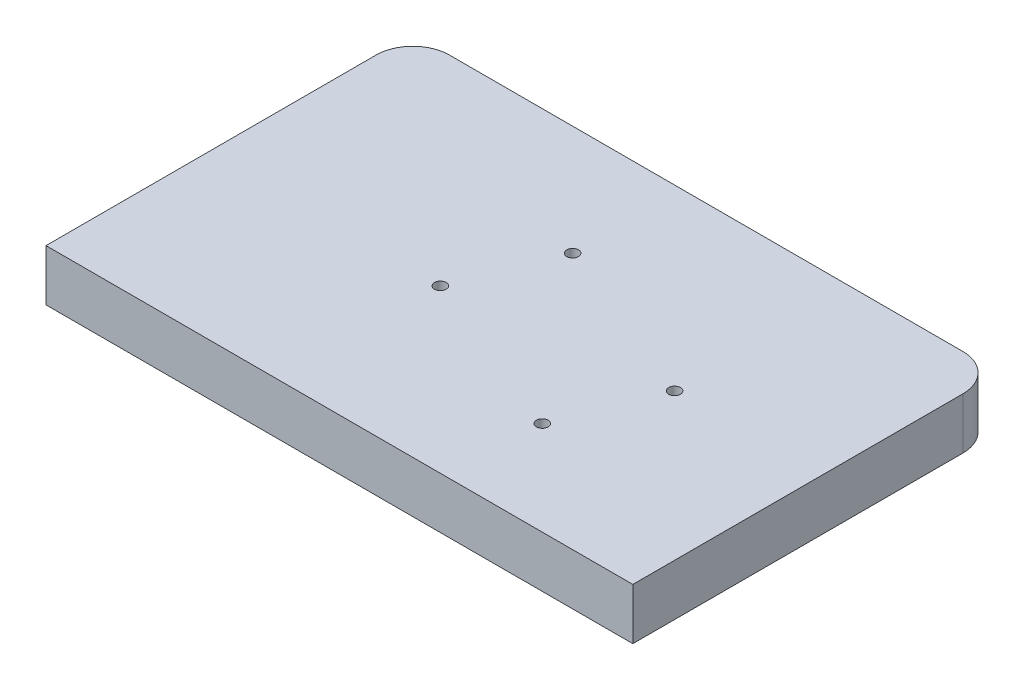
SolidWorks part; units mm, degrees
material "Pine"
ref_plane "Front Plane" through (0, 0, 0) normal (0, 0, 1) x (1, 0, 0)
ref_plane "Top Plane" through (0, 0, 0) normal (0, 1, 0) x (1, 0, 0)
ref_plane "Right Plane" through (0, 0, 0) normal (1, 0, 0) x (0, 0, -1)
sketch "Sketch2" plane through (0, 0, 0) normal (0, 1, 0) x (1, 0, 0)
  line L1 (-101.6, 63.5) -> (101.6, 63.5)
  line L2 (-101.6, 63.5) -> (-101.6, -63.5)
  line L3 (-101.6, -63.5) -> (101.6, -63.5)
  line L4 (101.6, 63.5) -> (101.6, -63.5)
  line L5 (-101.6, 63.5) -> (101.6, -63.5) construction
  line L6 (-101.6, -63.5) -> (101.6, 63.5) construction
  point P0 (0, 0)
  dimension "D1" = 203.2
  dimension "D2" = 127
extrude "Boss-Extrude2" add sketch "Sketch2" along normal blind 17.78
fillet "Fillet1" radius 12.7 2 edges at (-101.6, 8.89, -63.5) (101.6, 8.89, -63.5)
sketch "Sketch5" plane through (0, 0, 0) normal (0, -1, 0) x (1, 0, 0)
  line L0 (-101.6, 63.5) -> (101.6, 63.5) construction
  line L1 (101.6, 63.5) -> (101.6, -50.8) construction
  line L2 (-101.6, -50.8) -> (-101.6, 63.5) construction
  circle A0 centre (50.8, 49.8348) radius 2.0828
  circle A1 centre (33.5788, 25.0698) radius 2.0828
  circle A2 centre (-50.8, 25.0698) radius 2.0828
  circle A3 centre (-33.5788, 49.8348) radius 2.0828
  dimension "D1" = 4.1656
  dimension "D2" = 13.6652
  dimension "D3" = 38.4302
  dimension "D4" = 17.2212
  dimension "D5" = 38.4302
  dimension "D6" = 13.6652
  dimension "D7" = 17.2212
  dimension "D8" = 50.8
  dimension "D9" = 50.8
extrude "Cut-Extrude2" cut sketch "Sketch5" against normal blind 12.7
sketch "Sketch6" plane through (0, 17.78, 0) normal (0, 1, 0) x (1, 0, 0)
  line L0 (37.6825, -30.9402) -> (-21.2516, -30.9402) construction
  line L2 (88.9, 63.5) -> (-88.9, 63.5) construction
  line L3 (101.6, -63.5) -> (101.6, 50.8) construction
  line L4 (-8.1341, 25.4) -> (50.8, 1.7564) construction
  line L5 (37.6825, -30.9402) -> (50.8, 1.7564) construction
  line L6 (37.6825, -30.9402) -> (-21.2516, -7.2967) construction
  line L7 (-21.2516, -7.2967) -> (-8.1341, 25.4) construction
  circle A0 centre (-8.1341, 25.4) radius 2.032
  circle A3 centre (50.8, 1.7564) radius 2.032
  circle A4 centre (-21.2516, -7.2967) radius 2.032
  circle A5 centre (37.6825, -30.9402) radius 2.032
  dimension "D1" = 35.2298
  dimension "D2" = 63.5
  dimension "D3" = 63.5
  dimension "D4" = 35.2298
  dimension "D5" = 38.1
  dimension "D6" = 50.8
  dimension "D7" = 90
  dimension "D8" = 21.86
extrude "Cut-Extrude3" cut sketch "Sketch6" against normal blind 12.7
